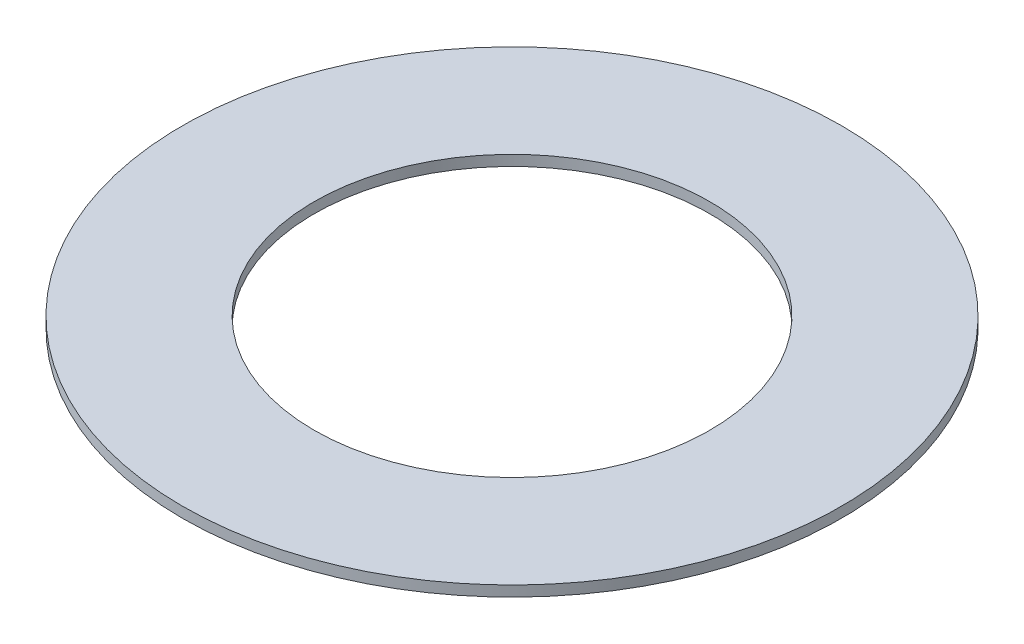
SolidWorks part; units mm, degrees
ref_plane "Front Plane" through (0, 0, 0) normal (0, 0, 1) x (1, 0, 0)
ref_plane "Top Plane" through (0, 0, 0) normal (0, 1, 0) x (1, 0, 0)
ref_plane "Right Plane" through (0, 0, 0) normal (1, 0, 0) x (0, 0, -1)
sketch "Sketch1" plane through (0, 0, 0) normal (0, 1, 0) x (1, 0, 0)
  circle A0 centre (0, 0) radius 2.3876
  circle A1 centre (0, 0) radius 3.9751
  dimension "D1" = 4.7752
  dimension "D2" = 7.9502
extrude "Boss-Extrude1" add sketch "Sketch1" along normal blind 0.127
